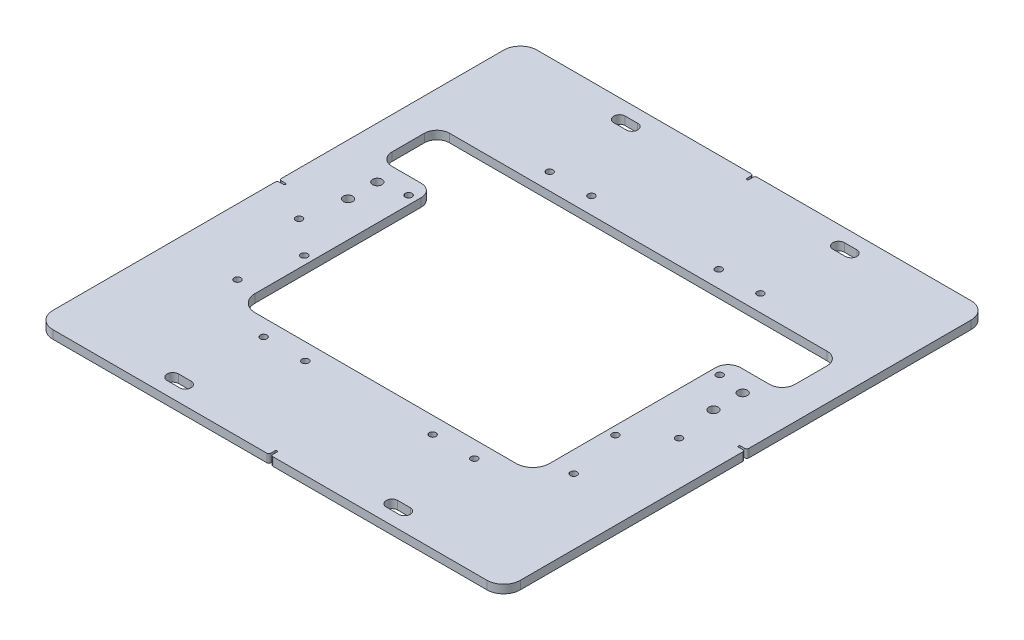
SolidWorks part; units mm, degrees
material "AISI Type 316L stainless steel"
ref_plane "Front Plane" through (0, 0, 0) normal (0, 0, 1) x (1, 0, 0)
ref_plane "Top Plane" through (0, 0, 0) normal (0, 1, 0) x (1, 0, 0)
ref_plane "Right Plane" through (0, 0, 0) normal (1, 0, 0) x (0, 0, -1)
sketch "Sketch2" plane through (0, 0, 0) normal (0, 1, 0) x (1, 0, 0)
  line L1 (-177.8, 184.15) -> (177.8, 184.15)
  line L2 (-177.8, 184.15) -> (-177.8, -184.15)
  line L3 (-177.8, -184.15) -> (177.8, -184.15)
  line L4 (177.8, 184.15) -> (177.8, -184.15)
  line L5 (-177.8, 184.15) -> (177.8, -184.15) construction
  line L6 (-177.8, -184.15) -> (177.8, 184.15) construction
  point P0 (0, 0)
  dimension "D1" = 355.6
  dimension "D2" = 368.3
extrude "Boss-Extrude1" add sketch "Sketch2" along normal blind 6.35
fillet "Fillet1" radius 12.7 4 edges at (-177.8, 3.175, -184.15) (-177.8, 3.175, 184.15) (177.8, 3.175, -184.15) (177.8, 3.175, 184.15)
sketch "Sketch3" plane through (0, 6.35, 0) normal (0, 1, 0) x (1, 0, 0)
  line L0 (165.1, 184.15) -> (-165.1, 184.15) construction
  line L1 (0, 184.15) -> (0, -184.15) construction
  line L2 (-165.1, -184.15) -> (165.1, -184.15) construction
  line L3 (-88.1063, 169.8625) -> (-78.5812, 169.8625) construction
  line L4 (-88.1063, 174.2281) -> (-78.5812, 174.2281)
  line L5 (-88.1063, 165.4969) -> (-78.5812, 165.4969)
  line L6 (88.1063, 169.8625) -> (78.5812, 169.8625) construction
  line L7 (88.1063, 165.4969) -> (78.5812, 165.4969)
  line L8 (88.1063, 174.2281) -> (78.5812, 174.2281)
  line L9 (-88.1062, -169.8625) -> (-78.5812, -169.8625) construction
  line L10 (-88.1062, -165.4969) -> (-78.5812, -165.4969)
  line L11 (-88.1062, -174.2281) -> (-78.5812, -174.2281)
  line L12 (78.5813, -169.8625) -> (88.1063, -169.8625) construction
  line L13 (78.5813, -165.4969) -> (88.1063, -165.4969)
  line L14 (78.5813, -174.2281) -> (88.1063, -174.2281)
  arc A4 (-88.1063, 174.2281) -> (-88.1063, 165.4969) centre (-88.1063, 169.8625) ccw
  arc A5 (-78.5812, 165.4969) -> (-78.5812, 174.2281) centre (-78.5812, 169.8625) ccw
  arc A6 (88.1063, 165.4969) -> (88.1063, 174.2281) centre (88.1063, 169.8625) ccw
  arc A7 (78.5812, 174.2281) -> (78.5812, 165.4969) centre (78.5812, 169.8625) ccw
  arc A8 (-88.1062, -165.4969) -> (-88.1062, -174.2281) centre (-88.1062, -169.8625) ccw
  arc A9 (-78.5812, -174.2281) -> (-78.5812, -165.4969) centre (-78.5812, -169.8625) ccw
  arc A10 (78.5813, -165.4969) -> (78.5813, -174.2281) centre (78.5813, -169.8625) ccw
  arc A11 (88.1063, -174.2281) -> (88.1063, -165.4969) centre (88.1063, -169.8625) ccw
  point P16 (-83.3438, 169.8625)
  point P23 (83.3438, 169.8625)
  point P28 (-83.3437, -169.8625)
  point P35 (83.3438, -169.8625)
  dimension "D2" = 4.3656
  dimension "D3" = 14.2875
  dimension "D5" = 88.1063
  dimension "D6" = 88.1063
  dimension "D7" = 14.2875
  dimension "D8" = 88.1063
  dimension "D11" = 14.2875
  dimension "D9" = 88.1063
  dimension "D4" = 14.2875
  dimension "D10" = 9.525
extrude "MOUNTING HOLES" cut sketch "Sketch3" against normal through all
sketch "Sketch4" plane through (0, 6.35, 0) normal (0, 1, 0) x (1, 0, 0)
  line L0 (-177.8, 171.45) -> (-177.8, -171.45) construction
  line L1 (-99.281, -96.106) -> (99.281, -96.106)
  line L2 (-111.981, -83.406) -> (-111.981, 42.8689)
  line L3 (-143.6687, 96.106) -> (143.6687, 96.106)
  line L4 (111.981, -83.406) -> (111.981, 42.8688)
  line L5 (-111.981, -96.106) -> (111.981, 96.106) construction
  line L6 (-111.981, 96.106) -> (111.981, -96.106) construction
  line L7 (-143.6687, 52.3939) -> (-121.506, 52.3939)
  line L8 (165.1, 184.15) -> (-165.1, 184.15) construction
  line L9 (-153.1937, 86.581) -> (-153.1937, 61.9189)
  line L10 (143.6687, 52.3939) -> (121.506, 52.3939)
  line L11 (153.1937, 61.9189) -> (153.1937, 86.581)
  line L12 (177.8, -171.45) -> (177.8, 171.45) construction
  arc A0 (-99.281, -96.106) -> (-111.981, -83.406) centre (-99.281, -83.406) cw
  arc A1 (99.281, -96.106) -> (111.981, -83.406) centre (99.281, -83.406) ccw
  arc A4 (143.6687, 96.106) -> (153.1937, 86.581) centre (143.6687, 86.581) cw
  arc A5 (143.6687, 52.3939) -> (153.1937, 61.9189) centre (143.6687, 61.9189) ccw
  arc A6 (121.506, 52.3939) -> (111.981, 42.8688) centre (121.506, 42.8689) ccw
  arc A7 (-121.506, 52.3939) -> (-111.981, 42.8689) centre (-121.506, 42.8689) cw
  arc A8 (-153.1937, 61.9189) -> (-143.6687, 52.3939) centre (-143.6687, 61.9189) ccw
  arc A9 (-143.6687, 96.106) -> (-153.1937, 86.581) centre (-143.6687, 86.581) ccw
  point P0 (0, 0)
  point P34 (-132.5874, 52.3939)
  dimension "D3" = 12.7
  dimension "D4" = 9.525
  dimension "D1" = 65.819
  dimension "D2" = 88.044
  dimension "D5" = 131.7561
  dimension "D6" = 24.6063
  dimension "D7" = 24.6063
  dimension "D8" = 65.819
  dimension "D9" = 280.256
  dimension "D10" = 131.7561
extrude "PLUNGER CUTOUT" cut sketch "Sketch4" against normal through all
hole_wizard "1/4-20 Tapped Hole2" positions "Sketch8" profile "Sketch9" tap size "1/4-20" standard "ANSI Inch" end condition through all
sketch "Sketch8" plane through (0, 6.35, 0) normal (0, 1, 0) x (1, 0, 0)
  line L0 (165.1, 184.15) -> (-165.1, 184.15) construction
  line L1 (-177.8, 171.45) -> (-177.8, -171.45) construction
  line L2 (177.8, -171.45) -> (177.8, 171.45) construction
  line L3 (-165.1, -184.15) -> (165.1, -184.15) construction
  point P7 (-80.1675, -108.8187)
  point P9 (-48.4175, -108.8187)
  point P11 (48.4175, -108.8187)
  point P13 (80.1675, -108.8187)
  point P15 (80.1675, 108.8187)
  point P17 (48.4175, 108.8187)
  point P19 (-48.4175, 108.8187)
  point P21 (-80.1675, 108.8187)
  dimension "D3" = 31.75
  dimension "D1" = 75.3313
  dimension "D2" = 97.6325
  dimension "D4" = 97.6325
  dimension "D5" = 31.75
  dimension "D6" = 75.3313
sketch "Sketch9" plane through (-80.1675, 6.35, 108.8187) normal (1, 0, 0) x (0, 0, 1)
  line L0 (0, 0) -> (0, 6.35)
  line L1 (0, 6.35) -> (2.5527, 6.35)
  line L2 (2.5527, 6.35) -> (2.5527, 0)
  line L5 (2.5527, 0) -> (0, 0)
  line L11 (0, -6.35) -> (0, 107.95) construction
  dimension "Thru Tap Drill Dia." = 5.1054
  dimension "Thru Tap Drill Depth" = 6.35
cosmetic thread "Hole Thread9" parameters "D2"=6.35
cosmetic thread "Hole Thread10" parameters "D2"=6.35
cosmetic thread "Hole Thread11" parameters "D2"=6.35
cosmetic thread "Hole Thread12" parameters "D2"=6.35
cosmetic thread "Hole Thread13" parameters "D2"=6.35
cosmetic thread "Hole Thread14" parameters "D2"=6.35
cosmetic thread "Hole Thread15" parameters "D2"=6.35
cosmetic thread "Hole Thread16" parameters "D2"=6.35
sketch "Sketch10" plane through (0, 6.35, 0) normal (0, 1, 0) x (1, 0, 0)
  line L0 (165.1, 184.15) -> (-165.1, 184.15) construction
  line L1 (177.8, -171.45) -> (177.8, 171.45) construction
  line L2 (-165.1, -184.15) -> (165.1, -184.15) construction
  line L3 (-177.8, 171.45) -> (-177.8, -171.45) construction
  line L4 (0, 184.15) -> (0, -184.15) construction
  line L5 (-177.8, 0) -> (177.8, 0) construction
  line L6 (-0.7937, -179.3875) -> (-0.7937, -185.0078)
  line L7 (-0.7937, -185.0078) -> (0.7937, -185.0078)
  line L8 (0.7937, -179.3875) -> (0.7937, -185.0078)
  line L9 (-173.0375, 0.7937) -> (-178.8092, 0.7937)
  line L10 (-178.8092, 0.7937) -> (-178.8092, -0.7938)
  line L11 (-173.0375, -0.7937) -> (-178.8092, -0.7938)
  line L12 (173.0375, 0.7938) -> (178.4654, 0.7938)
  line L13 (178.4654, 0.7938) -> (178.4654, -0.7937)
  line L14 (173.0375, -0.7937) -> (178.4654, -0.7937)
  line L15 (-0.7937, 179.3875) -> (-0.7937, 184.7937)
  line L16 (-0.7937, 184.7937) -> (0.7937, 184.7937)
  line L17 (0.7937, 179.3875) -> (0.7937, 184.7937)
  arc A0 (-0.7937, 179.3875) -> (0.7937, 179.3875) centre (0, 179.3875) ccw
  arc A1 (-173.0375, -0.7937) -> (-173.0375, 0.7937) centre (-173.0375, 0) ccw
  arc A2 (0.7937, -179.3875) -> (-0.7937, -179.3875) centre (0, -179.3875) ccw
  arc A3 (173.0375, 0.7938) -> (173.0375, -0.7937) centre (173.0375, 0) ccw
  dimension "D1" = 1.5875
  dimension "D2" = 4.7625
  dimension "D3" = 4.7625
  dimension "D4" = 4.7625
  dimension "D5" = 4.7625
extrude "CENTERING MARKERS" cut sketch "Sketch10" against normal through all
fillet "Fillet2" radius 1.5875 8 edges at (0.7937, 3.175, 184.15) (-0.7937, 3.175, 184.15) (177.8, 3.175, -0.7938) (177.8, 3.175, 0.7937) (-0.7937, 3.175, -184.15) (0.7937, 3.175, -184.15) (-177.8, 3.175, -0.7938) (-177.8, 3.175, 0.7938)
hole_wizard "1/4-20 Tapped Hole5" positions "Sketch15" profile "Sketch16" tap size "1/4-20" standard "ANSI Inch" end condition through all
sketch "Sketch15" plane through (0, 6.35, 0) normal (0, 1, 0) x (1, 0, 0)
  point P0 (-144.526, -17.4752)
  point P3 (-127.8573, -80.9752)
  point P6 (-118.3323, -39.6875)
  point P9 (-118.3323, 39.6875)
  point P12 (118.3323, 39.6875)
  point P15 (118.3323, -39.6875)
  point P18 (144.526, -17.4752)
  point P21 (127.8573, -80.9752)
sketch "Sketch16" plane through (-144.526, 6.35, 17.4752) normal (1, 0, 0) x (0, 0, 1)
  line L0 (0, 0) -> (0, 6.35)
  line L1 (0, 6.35) -> (2.5527, 6.35)
  line L2 (2.5527, 6.35) -> (2.5527, 0)
  line L5 (2.5527, 0) -> (0, 0)
  line L11 (0, -6.35) -> (0, 107.95) construction
  dimension "Thru Tap Drill Dia." = 5.1054
  dimension "Thru Tap Drill Depth" = 6.35
cosmetic thread "Hole Thread25" parameters "D2"=6.35
cosmetic thread "Hole Thread26" parameters "D2"=6.35
cosmetic thread "Hole Thread27" parameters "D2"=6.35
cosmetic thread "Hole Thread28" parameters "D2"=6.35
cosmetic thread "Hole Thread29" parameters "D2"=6.35
cosmetic thread "Hole Thread30" parameters "D2"=6.35
cosmetic thread "Hole Thread31" parameters "D2"=6.35
cosmetic thread "Hole Thread32" parameters "D2"=6.35
chamfer "Chamfer1" [suppressed] distance 3.175 angle 45
sketch "Sketch17" plane through (0, 6.35, 0) normal (0, 1, 0) x (1, 0, 0)
  line L0 (-2.3813, 184.15) -> (-165.1, 184.15) construction
  line L1 (-177.8, 171.45) -> (-177.8, 2.3813) construction
  line L2 (177.8, 2.3813) -> (177.8, 171.45) construction
  line L3 (165.1, 184.15) -> (2.3813, 184.15) construction
  circle A0 centre (-138.9698, 36.5125) radius 3.5719
  circle A1 centre (-138.9698, 14.2875) radius 3.5719
  circle A2 centre (138.9698, 14.2875) radius 3.5719
  circle A3 centre (138.9698, 36.5125) radius 3.5719
  dimension "D1" = 7.1437
  dimension "D2" = 147.6375
  dimension "D3" = 38.8302
  dimension "D4" = 22.225
  dimension "D5" = 38.8302
  dimension "D7" = 22.225
  dimension "D6" = 147.6375
extrude "Cut-Extrude1" cut sketch "Sketch17" against normal through all
